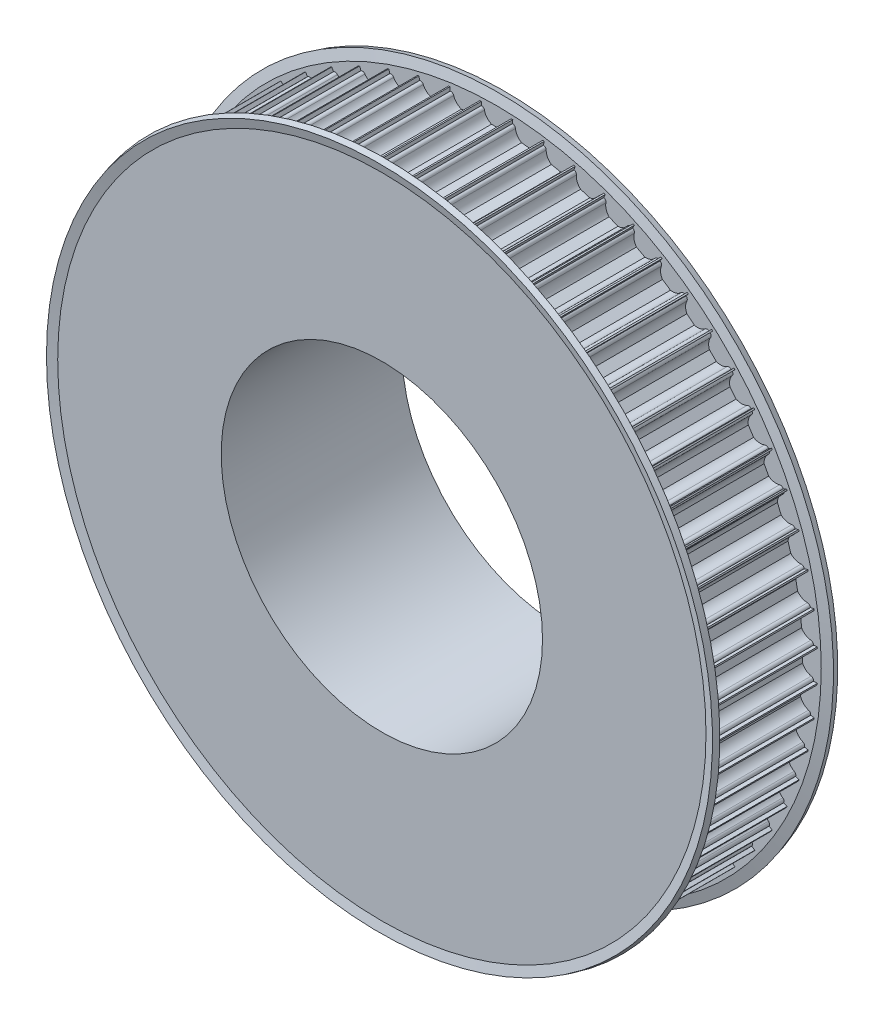
SolidWorks part; units mm, degrees
ref_plane "Front Plane" through (0, 0, 0) normal (0, 0, 1) x (1, 0, 0)
ref_plane "Top Plane" through (0, 0, 0) normal (0, 1, 0) x (1, 0, 0)
ref_plane "Right Plane" through (0, 0, 0) normal (1, 0, 0) x (0, 0, -1)
sketch "Sketch1" plane through (0, 0, 0) normal (1, 0, 0) x (0, 0, -1)
  line L0 (0, 0) -> (51.162, 0) construction
  line L1 (0, 40) -> (0, 80)
  line L2 (0, 80) -> (30, 80)
  line L3 (30, 80) -> (30, 55.5)
  line L4 (30, 55.5) -> (45, 55.5)
  line L5 (45, 55.5) -> (45, 40)
  line L6 (45, 40) -> (0, 40)
  point P7 (0, 0)
  dimension "D1" = 80
  dimension "D2" = 30
  dimension "D3" = 40
  dimension "D4" = 15
  dimension "D5" = 15.5
revolve "Revolve1" add sketch "Sketch1" angle 360 about L0
sketch "Sketch2" plane through (0, 0, 0) normal (0, 0, 1) x (1, 0, 0)
  line L5 (-3.6742, 79) -> (-3.75, 79)
  line L6 (-3.75, 79) -> (-3.75, 81)
  line L7 (-3.75, 81) -> (3.75, 81)
  line L8 (3.75, 81) -> (3.75, 79)
  line L9 (3.75, 79) -> (3.6742, 79)
  line L10 (-1.199, 76.25) -> (1.199, 76.25)
  arc A1 (-2.9394, 78.4) -> (-1.199, 76.25) centre (0, 79) ccw
  arc A2 (-2.9394, 78.4) -> (-3.6742, 79) centre (-3.6742, 78.25) ccw
  arc A3 (2.9394, 78.4) -> (3.6742, 79) centre (3.6742, 78.25) cw
  arc A4 (1.199, 76.25) -> (2.9394, 78.4) centre (0, 79) ccw
  point P9 (0, 81)
  point P13 (-3, 79)
  point P16 (3, 79)
  dimension "D1" = 3
  dimension "D2" = 79
  dimension "D4" = 0.75
  dimension "D5" = 0.75
  dimension "D7" = 2.75
  dimension "D3" = 7.5
  dimension "D6" = 2
extrude "Cut-Extrude1" cut sketch "Sketch2" against normal up to next (30 mm away)
pattern_circular "CirPattern1" count 64 over 360 about axis through (0, 0, 0) along (0, 0, 1) of "Cut-Extrude1"
sketch "Sketch3" plane through (0, 0, 0) normal (1, 0, 0) x (0, 0, -1)
  line L0 (15, -40.9775) -> (15, -10.6098) construction
  line L1 (30, -40.9775) -> (0, -40.9775) construction
  line L2 (30, -10.6098) -> (0, -10.6098) construction
  line L3 (30, 55.5) -> (30, 80.7025)
  line L4 (30, 80.7025) -> (30.592, 82.9118)
  line L5 (30.592, 82.9118) -> (29.1431, 83.3)
  line L6 (29.1431, 83.3) -> (28.5, 80.9)
  line L7 (28.5, 80.9) -> (28.5, 55.5)
  line L8 (28.5, 55.5) -> (30, 55.5)
  line L9 (45, 55.5) -> (30, 55.5) construction
  line L10 (1.5, 80.9) -> (1.5, 55.5)
  line L11 (0.8569, 83.3) -> (1.5, 80.9)
  line L12 (-0.592, 82.9118) -> (0.8569, 83.3)
  line L13 (0, 80.7025) -> (-0.592, 82.9118)
  line L14 (0, 55.5) -> (0, 80.7025)
  line L15 (1.5, 55.5) -> (0, 55.5)
  line L16 (0, 0) -> (-8.7217, 0) construction
  dimension "D1" = 15
  dimension "D2" = 1.5
  dimension "D3" = 25.4
  dimension "D4" = 2.4
revolve "Revolve2" add sketch "Sketch3" angle 360 about L16
